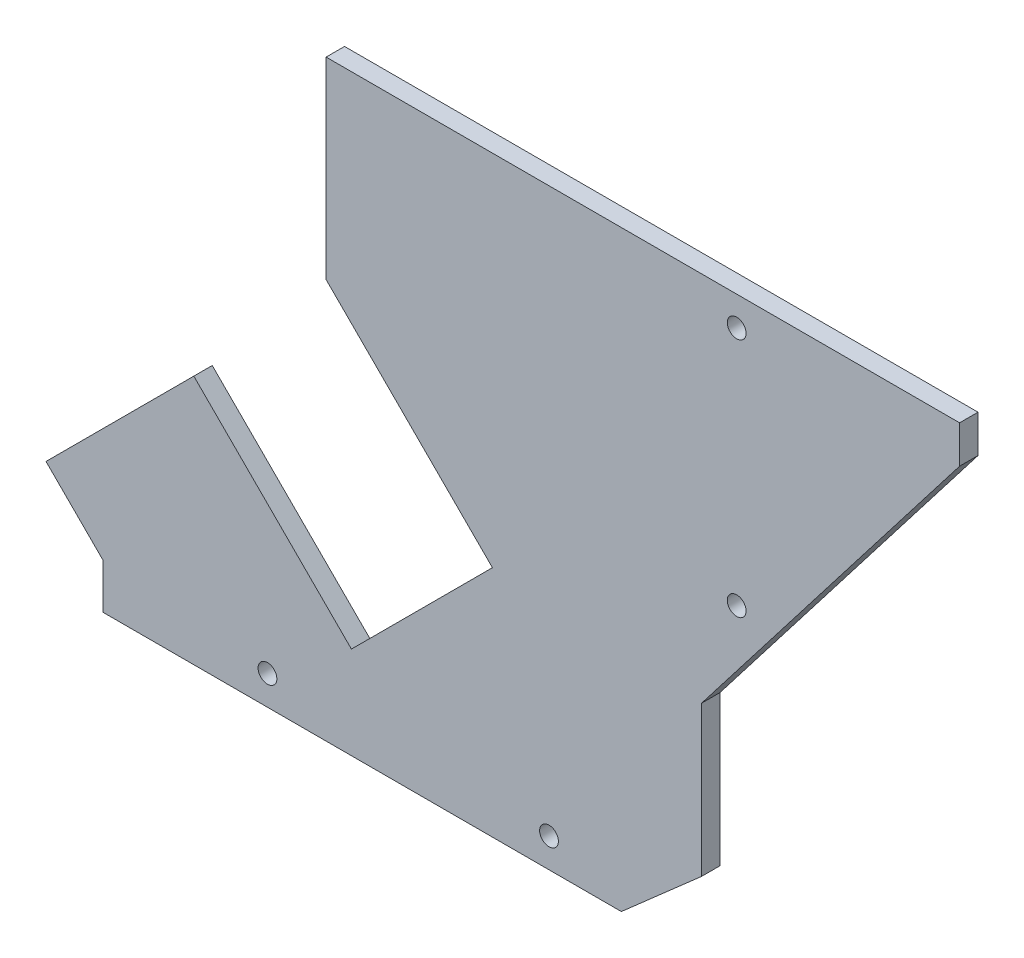
SolidWorks part; units mm, degrees
ref_plane "Front" through (0, 0, 0) normal (0, 0, 1) x (1, 0, 0)
ref_plane "Top" through (0, 0, 0) normal (0, 1, 0) x (1, 0, 0)
ref_plane "Right" through (0, 0, 0) normal (1, 0, 0) x (0, 0, -1)
sketch "Sketch2" plane through (0, 0, 0) normal (0, 0, 1) x (1, 0, 0)
  line L6 (0, -5) -> (5, -5) construction
  line L7 (0, 0) -> (0, -5) construction
  line L8 (-14, -55.5001) -> (-14, -51.6716)
  line L9 (37, -36.7042) -> (37, -49.4918)
  line L10 (7.1568, -47.6275) -> (19.1776, -35.6067)
  line L11 (5, -5) -> (5, -21.429)
  line L12 (5, -5) -> (59, -5)
  line L14 (-14, -51.6716) -> (-18.8787, -46.7929)
  line L15 (59, -8.2042) -> (59, -5)
  line L16 (-18.8787, -46.7929) -> (-6.2782, -34.1925)
  line L17 (19.1776, -35.6067) -> (5, -21.429)
  line L18 (59, -8.2042) -> (37, -36.7042)
  line L19 (30.1656, -55.5001) -> (37, -49.4918)
  line L20 (-14, -55.5001) -> (30.1656, -55.5001)
  line L21 (7.1568, -47.6275) -> (-6.2782, -34.1925)
extrude "Boss-Extrude1" add sketch "Sketch2" along normal blind 1.57
sketch "Sketch4" plane through (0, 0, 1.57) normal (0, 0, 1) x (1, 0, 0)
  circle A0 centre (39.9998, -7.5) radius 0.8
  circle A1 centre (39.9999, -27.9999) radius 0.8
  circle A2 centre (24.0001, -53) radius 0.8
  circle A3 centre (0.0001, -53) radius 0.8
extrude "Cut-Extrude1" cut sketch "Sketch4" against normal through all
